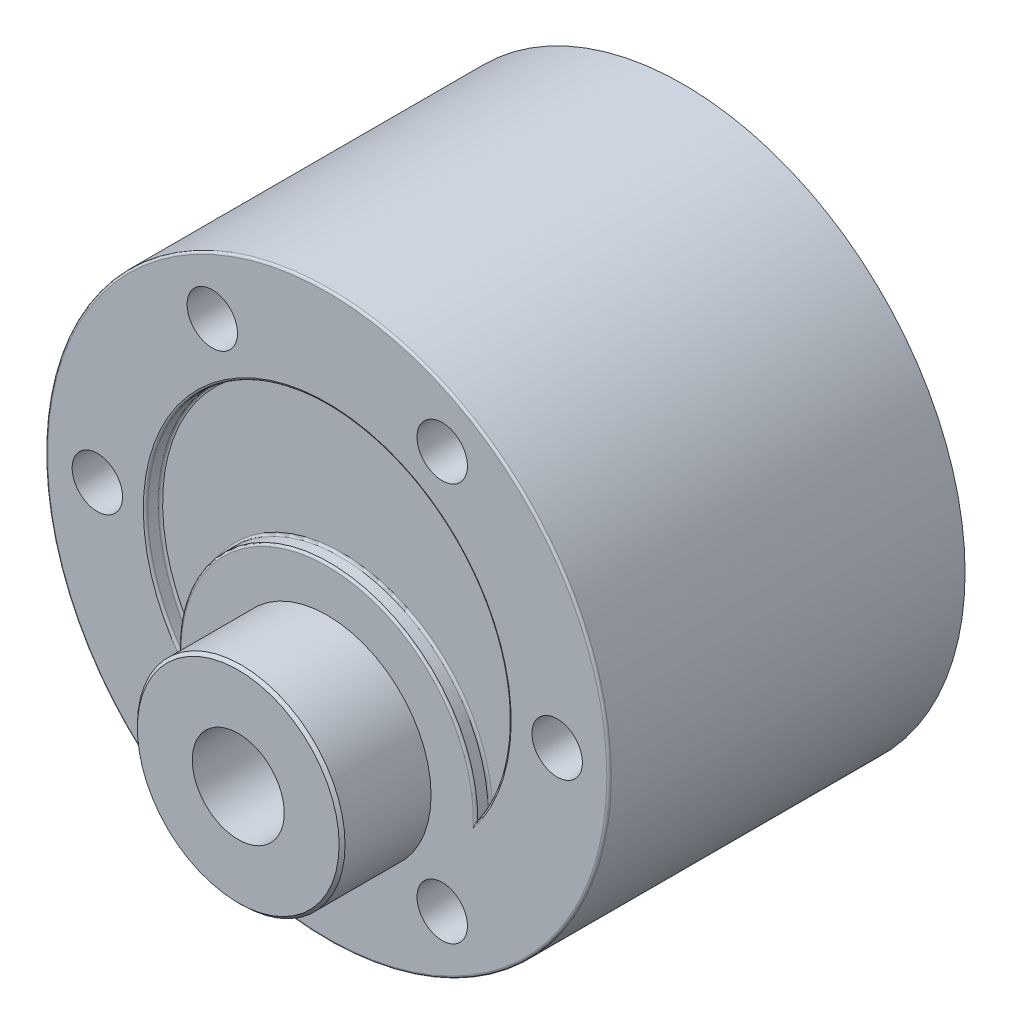
SolidWorks part; units mm, degrees
material "Chrome Stainless Steel"
ref_plane "Front Plane" through (0, 0, 0) normal (0, 0, 1) x (1, 0, 0)
ref_plane "Top Plane" through (0, 0, 0) normal (0, 1, 0) x (1, 0, 0)
ref_plane "Right Plane" through (0, 0, 0) normal (1, 0, 0) x (0, 0, -1)
sketch "Sketch1" plane through (0, 0, 0) normal (0, 0, 1) x (1, 0, 0)
  circle A0 centre (0, 0) radius 19
  dimension "D1" = 38
extrude "Boss-Extrude1" add sketch "Sketch1" along normal blind 24
sketch "Sketch3" plane through (0, 0, 24) normal (0, 0, 1) x (1, 0, 0)
  circle A0 centre (0, 0) radius 12.25
  dimension "D1" = 24.5
extrude "Cut-Extrude1" cut sketch "Sketch3" against normal blind 1
sketch "Sketch4" plane through (0, 0, 23) normal (0, 0, 1) x (1, 0, 0)
  circle A0 centre (0, -7) radius 10
extrude "Boss-Extrude4" add sketch "Sketch4" along normal blind 1
sketch "Sketch9" plane through (0, 0, 24) normal (0, 0, 1) x (1, 0, 0)
  circle A0 centre (0, -7) radius 7
extrude "Boss-Extrude5" add sketch "Sketch9" along normal blind 6
sketch "Sketch10" plane through (0, 0, 30) normal (0, 0, 1) x (1, 0, 0)
  circle A0 centre (0, -7) radius 3.1
  dimension "D2" = 6.2
  dimension "D1" = 7
extrude "Cut-Extrude2" cut sketch "Sketch10" against normal blind 20
hole_wizard "M3 Clearance Hole1" positions "Sketch19" profile "Sketch18" hole size "M3" standard "ISO"
sketch "Sketch19" plane through (0, 0, 24) normal (0, 0, 1) x (1, 0, 0)
  point P0 (15.5, 0)
  point P2 (-15.5, 0)
  point P4 (-7.75, 13.4234)
  point P6 (7.75, 13.4234)
  point P8 (-7.75, -13.4234)
  point P10 (7.75, -13.4234)
  dimension "D1" = 15.5
  dimension "D2" = 15.5
  dimension "D3" = 15.5
  dimension "D4" = 15.5
  dimension "D5" = 15.5
  dimension "D6" = 15.5
sketch "Sketch18" plane through (15.5, 0, 24) normal (1, 0, 0) x (0, -1, 0)
  line L0 (0, 0) -> (0, 4.5215)
  line L1 (0, 4.5215) -> (1.7, 3.5)
  line L2 (1.7, 3.5) -> (1.7, 0)
  line L5 (1.7, 0) -> (0, 0)
  line L10 (0, 4.5215) -> (-1.7, 3.5) construction
  line L11 (0, -6.35) -> (0, 107.95) construction
  dimension "Hole Dia." = 3.4
  dimension "Hole Depth" = 3.5
  dimension "Drill Angle" = 118
fillet "Fillet1" radius 0.15 5 edges at (19, 0, 24) (0, 3, 23) (0, 3, 24) (0, 12.25, 23) (0, 12.25, 24)
chamfer "Chamfer1" distance 0.2 angle 45 1 edges at (7, -7, 30)
